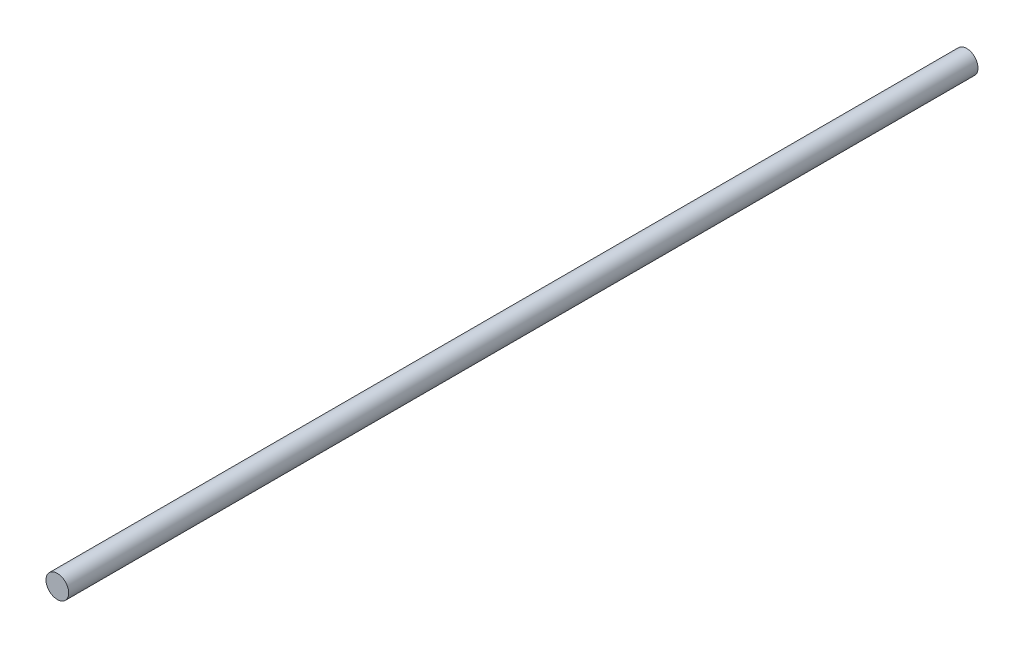
SolidWorks part; units mm, degrees
ref_plane "Front Plane" through (0, 0, 0) normal (0, 0, 1) x (1, 0, 0)
ref_plane "Top Plane" through (0, 0, 0) normal (0, 1, 0) x (1, 0, 0)
ref_plane "Right Plane" through (0, 0, 0) normal (1, 0, 0) x (0, 0, -1)
sketch "Sketch1" plane through (0, 0, 0) normal (0, 0, 1) x (1, 0, 0)
  circle A0 centre (0, 0) radius 3
  dimension "D1" = 6
extrude "Boss-Extrude1" add sketch "Sketch1" along normal blind 240
